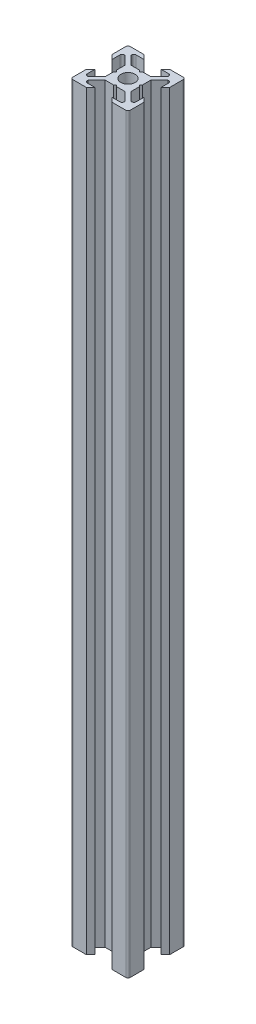
SolidWorks part; units mm, degrees
ref_plane "Face" through (0, 0, 0) normal (0, 0, 1) x (1, 0, 0)
ref_plane "Dessus" through (0, 0, 0) normal (0, 1, 0) x (1, 0, 0)
ref_plane "Droite" through (0, 0, 0) normal (1, 0, 0) x (0, 0, -1)
sketch "Esquisse1" plane through (0, 0, 0) normal (0, 1, 0) x (1, 0, 0)
  line L0 (0, 0) -> (0, 10) construction
  line L1 (0, 0) -> (-10, 0) construction
  line L2 (-10, 0) -> (-10, 10) construction
  line L3 (-10, 10) -> (0, 10) construction
  line L4 (0, 4) -> (-0.5, 4.5)
  line L5 (-0.5, 4.5) -> (-3.4393, 4.5)
  line L6 (-3.4393, 4.5) -> (-6.4393, 7.5)
  line L7 (-6.4393, 7.5) -> (-6.4393, 8.5)
  line L8 (-6.4393, 8.5) -> (-3, 8.5)
  line L9 (-3, 8.5) -> (-4.5, 10)
  line L10 (-4.5, 10) -> (-10, 10)
  line L11 (0, 0) -> (-10, 10) construction
  line L12 (-10, 4.5) -> (-10, 10)
  line L13 (-8.5, 3) -> (-10, 4.5)
  line L14 (-8.5, 6.4393) -> (-8.5, 3)
  line L15 (-7.5, 6.4393) -> (-8.5, 6.4393)
  line L16 (-4.5, 3.4393) -> (-7.5, 6.4393)
  line L17 (-4.5, 0.5) -> (-4.5, 3.4393)
  line L18 (-4, 0) -> (-4.5, 0.5)
  line L19 (0, -4) -> (-0.5, -4.5)
  line L20 (-0.5, -4.5) -> (-3.4393, -4.5)
  line L21 (-4, 0) -> (-4.5, -0.5)
  line L22 (-4.5, -0.5) -> (-4.5, -3.4393)
  line L23 (-4.5, -3.4393) -> (-7.5, -6.4393)
  line L24 (-3.4393, -4.5) -> (-6.4393, -7.5)
  line L25 (-3, -8.5) -> (-4.5, -10)
  line L26 (-6.4393, -8.5) -> (-3, -8.5)
  line L27 (-6.4393, -7.5) -> (-6.4393, -8.5)
  line L28 (-7.5, -6.4393) -> (-8.5, -6.4393)
  line L29 (-4.5, -10) -> (-10, -10)
  line L30 (-10, -4.5) -> (-10, -10)
  line L31 (-8.5, -3) -> (-10, -4.5)
  line L32 (-8.5, -6.4393) -> (-8.5, -3)
  line L33 (8.5, -6.4393) -> (8.5, -3)
  line L34 (8.5, -3) -> (10, -4.5)
  line L35 (10, -4.5) -> (10, -10)
  line L36 (4.5, -10) -> (10, -10)
  line L37 (7.5, -6.4393) -> (8.5, -6.4393)
  line L38 (6.4393, -7.5) -> (6.4393, -8.5)
  line L39 (6.4393, -8.5) -> (3, -8.5)
  line L40 (3, -8.5) -> (4.5, -10)
  line L41 (3.4393, -4.5) -> (6.4393, -7.5)
  line L42 (4.5, -3.4393) -> (7.5, -6.4393)
  line L43 (4.5, -0.5) -> (4.5, -3.4393)
  line L44 (4, 0) -> (4.5, -0.5)
  line L45 (0.5, -4.5) -> (3.4393, -4.5)
  line L46 (0, -4) -> (0.5, -4.5)
  line L47 (4, 0) -> (4.5, 0.5)
  line L48 (4.5, 0.5) -> (4.5, 3.4393)
  line L49 (4.5, 3.4393) -> (7.5, 6.4393)
  line L50 (7.5, 6.4393) -> (8.5, 6.4393)
  line L51 (8.5, 6.4393) -> (8.5, 3)
  line L52 (8.5, 3) -> (10, 4.5)
  line L53 (10, 4.5) -> (10, 10)
  line L54 (4.5, 10) -> (10, 10)
  line L55 (3, 8.5) -> (4.5, 10)
  line L56 (6.4393, 8.5) -> (3, 8.5)
  line L57 (6.4393, 7.5) -> (6.4393, 8.5)
  line L58 (3.4393, 4.5) -> (6.4393, 7.5)
  line L59 (0.5, 4.5) -> (3.4393, 4.5)
  line L60 (0, 4) -> (0.5, 4.5)
  circle A0 centre (0, 0) radius 2.5
  dimension "D10" = 5
  dimension "D1" = 10
  dimension "D2" = 45
  dimension "D3" = 45
  dimension "D4" = 1.5
  dimension "D5" = 7
  dimension "D6" = 1
  dimension "D7" = 4.5
  dimension "D8" = 0.5
  dimension "D9" = 0.75
extrude "Extrusion1" add sketch "Esquisse1" along normal blind 262
fillet "Congé1" radius 0.75 12 edges at (-8.5, 131, -6.4393) (-6.4393, 131, -8.5) (8.5, 131, -6.4393) (6.4393, 131, -8.5) (-8.5, 131, 6.4393) (-6.4393, 131, 8.5) (8.5, 131, 6.4393) (6.4393, 131, 8.5) (10, 131, -10) (-10, 131, -10) (-10, 131, 10) (10, 131, 10)
